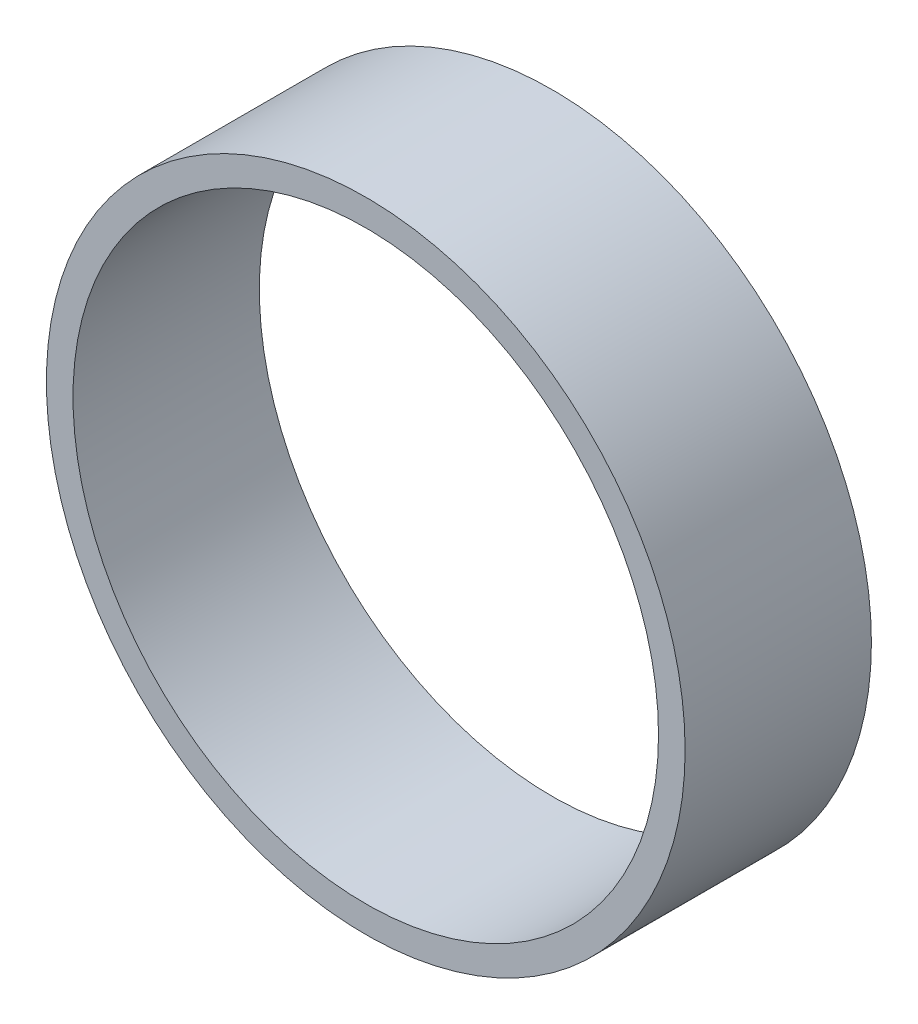
SolidWorks part; units mm, degrees
material "Plain Carbon Steel"
ref_plane "Front" through (0, 0, 0) normal (0, 0, 1) x (1, 0, 0)
ref_plane "Top" through (0, 0, 0) normal (0, 1, 0) x (1, 0, 0)
ref_plane "Right" through (0, 0, 0) normal (1, 0, 0) x (0, 0, -1)
ref_plane "Plane1" through (0, 0, 373.3022) normal (0, 0, 1) x (1, 0, 0)
sketch "Sketch2" plane through (0, 0, 373.3022) normal (0, 0, 1) x (1, 0, 0)
  circle A0 centre (0, 0) radius 76.2
  circle A1 centre (0, 0) radius 69.85
  dimension "D1" = 152.4
  dimension "D2" = 6.35
extrude "Extrude1" add sketch "Sketch2" against normal blind 44.45
